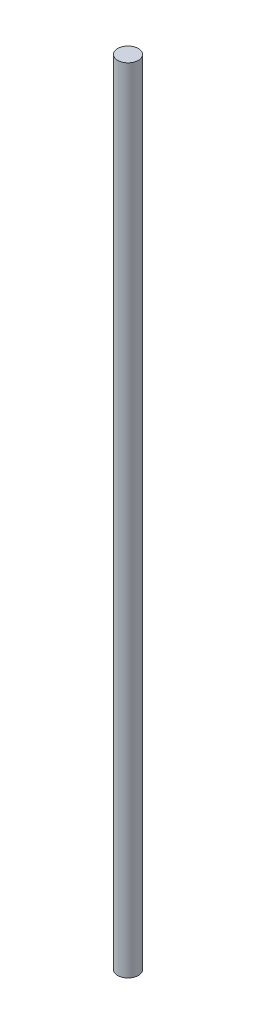
SolidWorks part; units mm, degrees
ref_plane "Front Plane" through (0, 0, 0) normal (0, 0, 1) x (1, 0, 0)
ref_plane "Top Plane" through (0, 0, 0) normal (0, 1, 0) x (1, 0, 0)
ref_plane "Right Plane" through (0, 0, 0) normal (1, 0, 0) x (0, 0, -1)
sketch "Sketch1" plane through (0, 0, 0) normal (0, 1, 0) x (1, 0, 0)
  circle A0 centre (0, 0) radius 3.9688
  dimension "D1" = 7.9375
extrude "Boss-Extrude1" add sketch "Sketch1" along normal blind 304.8
